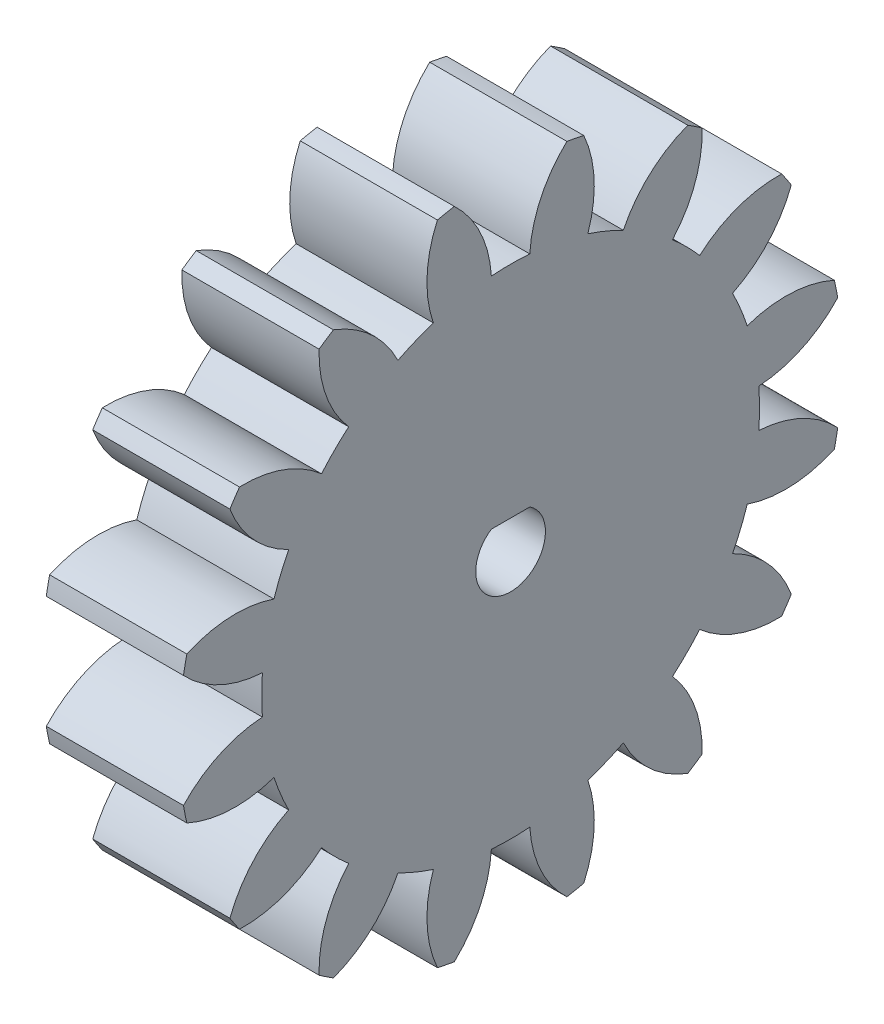
SolidWorks part; units mm, degrees
ref_plane "Plane1" through (0, 0, 0) normal (0, 0, 1) x (1, 0, 0)
ref_plane "Plane2" through (0, 0, 0) normal (0, 1, 0) x (1, 0, 0)
ref_plane "Plane3" through (0, 0, 0) normal (1, 0, 0) x (0, 0, -1)
sketch "HoldingSke" plane through (0, 0, 0) normal (0, 1, 0) x (1, 0, 0)
  line L0 (0, 0) -> (195.3284, -56.0095)
  line L1 (-15, 0) -> (100, 0) construction
  line L2 (0, 0) -> (-2.1039, 2.3779)
  line L3 (0, 0) -> (-11.863, 4.5341)
  line L4 (0, 0) -> (8.3015, 2.3804)
  line L5 (0, 0) -> (-47.5972, -17.7524)
  line L6 (0, 0) -> (-9.7909, -6.6059)
  line L7 (-2.1039, 2.3779) -> (8.8308, 51.9871)
  line L8 (-76.2, 54.61) -> (-75.184, 54.61)
  line L9 (-71.009, 38.7566) -> (-53.1078, 45.2721)
  line L10 (-76.2, 71.12) -> (104.1128, 71.12)
  line L11 (0, 0) -> (-11.811, 0)
  line L12 (-76.2, 101.6) -> (-76.0857, 101.6)
  line L13 (24.9733, 27.94) -> (52.9518, 28.4284)
  line L14 (24.9733, 27.94) -> (24.9746, 27.94)
  line L15 (24.9733, 27.94) -> (100.4006, 29.5858)
  circle A0 centre (0, 0) radius 0.3969
  circle A1 centre (0, 0) radius 21.43
  circle A2 centre (0, 0) radius 38.1
  circle A3 centre (0, 0) radius 0.3969
  dimension "MHD" = 42.86
  dimension "Hub_dia" = 76.2
  dimension "Bore" = 0.7937
  dimension "MBD" = 0.7937
  dimension "Num_teeth" = 16
  dimension "Pitch_radius" = 180.3128
  dimension "Pitch" = 203.2
  dimension "Width" = 11.811
  dimension "Overall_len" = 50.8
  dimension "Show_teeth" = 16
  dimension "Thickness" = 11.811
  dimension "OAL" = 50.8001
  dimension "T_dim" = 1.016
  dimension "Ap" = 20
  dimension "H" = 19.05
  dimension "Backlash" = 0.1143
  dimension "Addendum_fac" = 1
  dimension "Dedendum_fac" = 1.25
  dimension "Clearance_fac" = 0.25
  dimension "Dedendum_add" = 0.0013
sketch "BasProSke" plane through (0, 0, 0) normal (0, 1, 0) x (1, 0, 0)
  line L0 (-10, 0) -> (60, 0) construction
  line L1 (0, 0) -> (0, 28.575)
  line L2 (0, 0) -> (11.811, 0)
  line L3 (11.811, 0) -> (11.811, 28.575)
  line L4 (11.811, 28.575) -> (0, 28.575)
  dimension "Diameter" = 57.15
  dimension "Thickness" = 11.811
revolve "Base-Revolve" add sketch "BasProSke" angle 360 about L0
sketch "TooCutSke" plane through (0, 0, 0) normal (1, 0, 0) x (0, 0, -1)
  line L1 (0, 0) -> (0, 107) construction
  line L2 (0, 0) -> (-2.6895, 25.2572) construction
  line L3 (0, 0) -> (-9.8702, 49.6211) construction
  line L4 (-2.6895, 25.2572) -> (-4.9351, 24.8105) construction
  arc A0 (1.6538, 21.3661) -> (-1.6538, 21.3661) centre (0, 0) ccw
  arc A1 (4.8685, 28.183) -> (-4.8685, 28.183) centre (0, 0) ccw
  circle A2 centre (0, 0) radius 25.4 construction
  circle A3 centre (0, 0) radius 23.8682 construction
  arc A4 (-1.6538, 21.3661) -> (-4.8685, 28.183) centre (-11.7951, 20.7501) ccw
  arc A5 (4.8685, 28.183) -> (1.6538, 21.3661) centre (11.7951, 20.7501) ccw
  dimension "Root_dia" = 42.86
  dimension "Overcut_dia" = 57.2008
  dimension "Pitch_dia" = 50.8
  dimension "Base_dia" = 47.7364
  dimension "Flank_rad" = 10.16
  dimension "Half_ang" = 11.25
  dimension "Half_CT" = 2.2896
extrude "ToothCut" cut sketch "TooCutSke" along normal through all
fillet "Breaks" [suppressed] radius 0.0635
fillet "RootFillets" [suppressed] radius 0.795
pattern_circular "TeethCuts" count 16 every 22.5 about axis through (-10, 0, 0) along (1, 0, 0) of "ToothCut", "RootFillets", "Breaks"
sketch "HubNeaOneSke" plane through (0, 0, 0) normal (-1, 0, 0) x (0, 0, 1)
  circle A0 centre (0, 0) radius 21.43
  dimension "Diameter" = 42.86
extrude "HubNearOne" [suppressed] add sketch "HubNeaOneSke" along normal blind 38.9891
sketch "HubNeaBotSke" plane through (0, 0, 0) normal (-1, 0, 0) x (0, 0, 1)
  circle A0 centre (0, 0) radius 21.43
  dimension "Diameter" = 42.86
extrude "HubNearBoth" [suppressed] add sketch "HubNeaBotSke" along normal blind 19.4945
ref_plane "FarPln" through (11.811, 0, 0) normal (1, 0, 0) x (0, 0, -1)
sketch "HubFarSke" plane through (11.811, 0, 0) normal (1, 0, 0) x (0, 0, -1)
  circle A0 centre (0, 0) radius 21.43
  dimension "Diameter" = 42.86
extrude "HubFar" [suppressed] add sketch "HubFarSke" along normal blind 19.4945
sketch "BorSke" plane through (0, 0, 0) normal (1, 0, 0) x (0, 0, -1)
  circle A0 centre (0, 0) radius 0.3969
  dimension "Diameter" = 0.7937
extrude "Bore" cut sketch "BorSke" along normal mid plane 101.6001
sketch "KeySke" plane through (0, 0, 0) normal (1, 0, 0) x (0, 0, -1)
  line L0 (-0.127, 0) -> (-0.127, 0.6191)
  line L1 (-0.127, 0.6191) -> (0.127, 0.6191)
  line L2 (0.127, 0.6191) -> (0.127, 0)
  line L3 (0, 0) -> (0, 34) construction
  line L4 (-0.127, 0) -> (0.127, 0)
  dimension "Offset" = 0.6191
  dimension "Width" = 0.254
extrude "Keyway" [suppressed] cut sketch "KeySke" along normal mid plane 101.6001
pattern_circular "Keyway2" [suppressed] count 2 every 90 about axis through (-10, 0, 0) along (1, 0, 0)
sketch "Sketch1" plane through (11.811, 0, 0) normal (1, 0, 0) x (0, 0, -1)
  line L0 (-1.6583, 2.5) -> (1.6583, 2.5)
  arc A0 (-1.6583, 2.5) -> (1.6583, 2.5) centre (0, 0) ccw
  dimension "D1" = 6
  dimension "D2" = 2.5
extrude "Cut-Extrude1" cut sketch "Sketch1" against normal through all
equation "' \"Pitch@HoldingSke\" = 4"
equation "' \"Num_teeth@HoldingSke\" = 12"
equation "' \"Ap@HoldingSke\" =  20"
equation "' \"Width@HoldingSke\" = 0.5"
equation "' \"Hub_dia@HoldingSke\"= 1"
equation "' \"Overall_len@HoldingSke\" = 1.0"
equation "' \"Bore@HoldingSke\" = 0.75"
equation "' \"T_dim@HoldingSke\" = 0.85"
equation "' \"Width@KeySke\" = 0.25"
equation "' \"Show_teeth@HoldingSke\" = 13"
equation "' \"Backlash@HoldingSke\" = 0.009"
equation "' \"Addendum_fac@HoldingSke\" = 1.0"
equation "' \"Dedendum_fac@HoldingSke\" = 1.25"
equation "' \"Dedendum_add@HoldingSke\" = 0.00005"
equation "' \"Clearance_fac@HoldingSke\" = 0.25"
equation "' \"Pitch@HoldingSke\" = 0.5"
equation "' \"Num_teeth@HoldingSke\" = 23"
equation "' \"Show_teeth@HoldingSke\" = 23"
equation "' \"Backlash@HoldingSke\" = 0.0375"
equation "\"Overcut_dia@TooCutSke\" = (\"Num_teeth@HoldingSke\" + 2 * \"Addendum_fac@HoldingSke\") / \"Pitch@HoldingSke\" + 0.002"
equation "\"Pitch_dia@TooCutSke\" = \"Num_teeth@HoldingSke\" / \"Pitch@HoldingSke\""
equation "\"Base_dia@TooCutSke\" = \"Num_teeth@HoldingSke\" / \"Pitch@HoldingSke\" * cos((\"Ap@HoldingSke\"  * 3.14159265 / 180))"
equation "\"Root_dia@TooCutSke\" = (\"Num_teeth@HoldingSke\" + 2) / \"Pitch@HoldingSke\" - 2 * (\"Addendum_fac@HoldingSke\" + \"Dedendum_fac@HoldingSke\") / \"Pitch@HoldingSke\" - \"Dedendum_add@HoldingSke\" * 2"
equation "\"Half_ang@TooCutSke\" = 180 / \"Num_teeth@HoldingSke\""
equation "\"Half_CT@TooCutSke\" = \"Num_teeth@HoldingSke\" / \"Pitch@HoldingSke\" * sin((3.14159265 / 2 / \"Num_teeth@HoldingSke\")) / 2 - 7 * \"Backlash@HoldingSke\" / 4"
equation "\"Flank_rad@TooCutSke\" = \"Num_teeth@HoldingSke\" / \"Pitch@HoldingSke\" / 5"
equation "\"Radius@RootFillets\" = \"Clearance_fac@HoldingSke\" / \"Pitch@HoldingSke\" + \"Dedendum_add@HoldingSke\""
equation "\"Break_rad@Breaks\" = 0.02 / \"Pitch@HoldingSke\""
equation "\"Thickness@HoldingSke\" = \"Width@HoldingSke\""
equation "\"OAL@HoldingSke\" = \"Thickness@HoldingSke\""
equation "\"MHD@HoldingSke\" = (\"Num_teeth@HoldingSke\" + 2) / \"Pitch@HoldingSke\" - 2 * (\"Addendum_fac@HoldingSke\" + \"Dedendum_fac@HoldingSke\")  / \"Pitch@HoldingSke\" - \"Dedendum_add@HoldingSke\" * 2"
equation "\"MBD@HoldingSke\" = (\"Num_teeth@HoldingSke\" + 2) / \"Pitch@HoldingSke\" - 2 * (\"Addendum_fac@HoldingSke\" + \"Dedendum_fac@HoldingSke\")  / \"Pitch@HoldingSke\" - \"Dedendum_add@HoldingSke\" * 2 - 0.002"
equation "\"MHD@HoldingSke\" = ((sgn( \"MHD@HoldingSke\" - \"Hub_dia@HoldingSke\" )-1)*( \"MHD@HoldingSke\" - \"Hub_dia@HoldingSke\" ))/-2+ \"Hub_dia@HoldingSke\""
equation "\"MBD@HoldingSke\" = ((sgn( \"MBD@HoldingSke\" - \"Bore@HoldingSke\" )-1)*( \"MBD@HoldingSke\" - \"Bore@HoldingSke\" ))/-2+ \"Bore@HoldingSke\""
equation "\"OAL@HoldingSke\" = ((sgn( \"OAL@HoldingSke\" - \"Overall_len@HoldingSke\" )+1)*( \"OAL@HoldingSke\" - \"Overall_len@HoldingSke\" ))/2 + \"Overall_len@HoldingSke\" + 0.000002"
equation "\"Num_teeth@TeethCuts\" = int( \"Show_teeth@HoldingSke\" ) + 1"
equation "\"Num_teeth@TeethCuts\" = ((sgn( \"Num_teeth@TeethCuts\" - \"Num_teeth@HoldingSke\" )-1)*( \"Num_teeth@TeethCuts\" - \"Num_teeth@HoldingSke\" ))/-2+ \"Num_teeth@HoldingSke\""
equation "\"Num_teeth@TeethCuts\" = ((sgn( \"Num_teeth@TeethCuts\" - 2.0)+1)*( \"Num_teeth@TeethCuts\" - 2.0))/2 +2.0"
equation "\"Angle@TeethCuts\" = 360.0 / \"Num_teeth@HoldingSke\""
equation "\"Diameter@BasProSke\" = (\"Num_teeth@HoldingSke\" + 2 * \"Addendum_fac@HoldingSke\") / \"Pitch@HoldingSke\""
equation "\"Thickness@BasProSke\"  = \"Thickness@HoldingSke\""
equation "' \"Fillet_rad@BasProSke\" =  \"Thickness@HoldingSke\" * 0.05"
equation "\"MHD@HoldingSke\" = ((sgn( \"MHD@HoldingSke\" - \"Root_dia@TooCutSke\" )-1)*( \"MHD@HoldingSke\" - \"Root_dia@TooCutSke\" ))/-2+ \"Root_dia@TooCutSke\""
equation "\"Diameter@HubNeaOneSke\" = \"MHD@HoldingSke\""
equation "\"Length@HubNearOne\" = \"OAL@HoldingSke\" - \"Thickness@BasProSke\""
equation "\"Diameter@HubNeaBotSke\" = \"MHD@HoldingSke\""
equation "\"Length@HubNearBoth\" = ( \"OAL@HoldingSke\" - \"Thickness@BasProSke\" ) / 2.0"
equation "\"Thickness@FarPln\" = \"Thickness@BasProSke\""
equation "\"Diameter@HubFarSke\" = \"MHD@HoldingSke\""
equation "\"Length@HubFar\" = ( \"OAL@HoldingSke\" - \"Thickness@BasProSke\" ) / 2.0"
equation "\"Diameter@BorSke\" = \"MBD@HoldingSke\""
equation "\"D1@Bore\" = \"OAL@HoldingSke\" * 2.0"
equation "\"D1@Keyway\" = \"OAL@HoldingSke\" * 2.0"
equation "\"Offset@KeySke\" = \"T_dim@HoldingSke\" - \"MBD@HoldingSke\" / 2.0"
